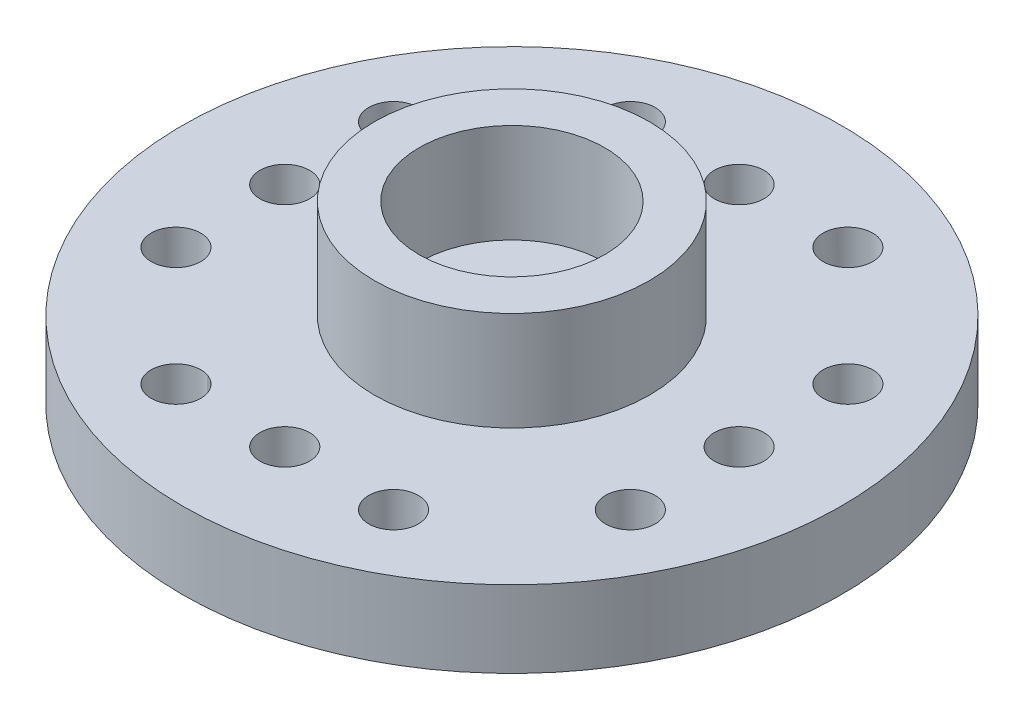
SolidWorks part; units mm, degrees
ref_plane "前视基准面" through (0, 0, 0) normal (0, 0, 1) x (1, 0, 0)
ref_plane "上视基准面" through (0, 0, 0) normal (0, 1, 0) x (1, 0, 0)
ref_plane "右视基准面" through (0, 0, 0) normal (1, 0, 0) x (0, 0, -1)
other "Configuration Table"
sketch "草图1" plane through (0, 0, 0) normal (0, 1, 0) x (1, 0, 0)
  circle A0 centre (0, 0) radius 10.3
  dimension "D1" = 20.6
extrude "凸台-拉伸1" add sketch "草图1" along normal blind 2.4
sketch "草图2" plane through (0, 2.4, 0) normal (0, 1, 0) x (1, 0, 0)
  circle A0 centre (0, 0) radius 4.3
  circle A1 centre (0, 0) radius 2.9
  dimension "D1" = 8.6
  dimension "D2" = 5.8
extrude "凸台-拉伸2" add sketch "草图2" along normal blind 3.1 contours A0 | A1
sketch "草图3" plane through (0, 0, 0) normal (0, -1, 0) x (1, 0, 0)
  line L0 (0, 7.1) -> (3.4, 7.1)
  line L1 (-7.1, 7.1) -> (7.1, 7.1)
  line L2 (-7.1, 7.1) -> (-7.1, -7.1)
  line L3 (-7.1, -7.1) -> (7.1, -7.1)
  line L4 (7.1, 7.1) -> (7.1, -7.1)
  line L5 (-7.1, 7.1) -> (7.1, -7.1) construction
  line L6 (-7.1, -7.1) -> (7.1, 7.1) construction
  line L7 (7.1, 0) -> (7.1, 3.4)
  line L8 (0, -7.1) -> (3.4, -7.1)
  line L9 (-7.1, 0) -> (-7.1, 3.4)
  circle A0 centre (0, 0) radius 7.1
  circle A1 centre (0, 7.1) radius 0.775
  circle A2 centre (0, -7.1) radius 0.775
  circle A3 centre (7.1, 0) radius 0.775
  circle A4 centre (-7.1, 0) radius 0.775
  circle A5 centre (3.4, 7.1) radius 0.775
  circle A6 centre (7.1, 3.4) radius 0.775
  circle A7 centre (3.4, -7.1) radius 0.775
  circle A8 centre (-7.1, 3.4) radius 0.775
  circle A9 centre (0, 0) radius 1.4
  dimension "D1" = 14.2
  dimension "D2" = 1.55
  dimension "D3" = 1.55
  dimension "D4" = 1.55
  dimension "D5" = 1.55
  dimension "D11" = 1.55
  dimension "D12" = 1.55
  dimension "D13" = 1.55
  dimension "D14" = 1.55
  dimension "D15" = 2.8
  dimension "D6" = 3.4
  dimension "D7" = 3.4
  dimension "D8" = 3.4
  dimension "D9" = 3.4
  dimension "D10" = 14.2
extrude "切除-拉伸1" cut sketch "草图3" against normal up to next (2.4 mm away) contours L0 A5 A0 L1 | L1 A5 L0 | L0 A1 L1 | A0 A1 | L4 A6 A0 | L4 A6 | A0 A6 | L4 A3 L7 | A0 A3 | A0 A7 | L3 A7 A0 | L3 A7 | L3 A2 | A0 A2 | L3 A2 A0 | A0 A2 L3 | A0 A3 L4 | L7 A3 A0 | A0 A1 L0 | L1 A1 A0 | L2 A8 | L2 A8 | A0 A4 | A0 A4 L9 | L9 A4 L2 | L2 A4 A0
mirror "镜向1" about plane through (0, 0, 0) normal (1, 0, 0) of "切除-拉伸1"
mirror "镜向2" about plane through (0, 0, 0) normal (0, 0, 1) of "切除-拉伸1"
sketch "草图4" plane through (0, 0, 0) normal (0, -1, 0) x (1, 0, 0)
  circle A0 centre (0, 0) radius 1.4
  dimension "D1" = 2.8
extrude "切除-拉伸2" cut sketch "草图4" against normal up to next
sketch3d "3D草图1"
  line L0 (0, 0, 0) -> (0, 4.5339, 0) construction
  point P3 (0, 0, 0)
